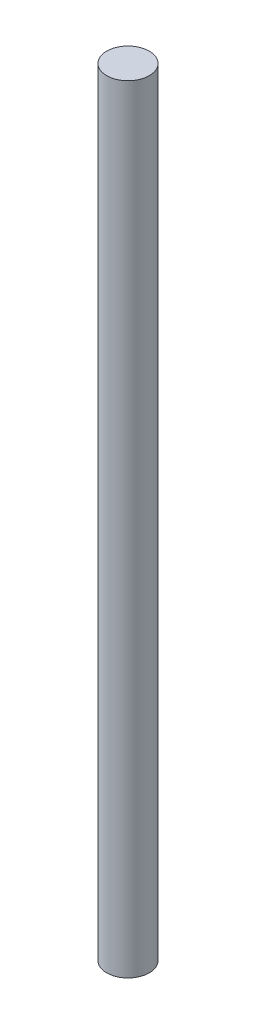
SolidWorks part; units mm, degrees
ref_plane "Front Plane" through (0, 0, 0) normal (0, 0, 1) x (1, 0, 0)
ref_plane "Top Plane" through (0, 0, 0) normal (0, 1, 0) x (1, 0, 0)
ref_plane "Right Plane" through (0, 0, 0) normal (1, 0, 0) x (0, 0, -1)
sketch "Sketch2" plane through (0, 0, 0) normal (0, 1, 0) x (1, 0, 0)
  circle A0 centre (0, 0) radius 2
  dimension "D1" = 4
extrude "Boss-Extrude1" add sketch "Sketch2" along normal blind 73
